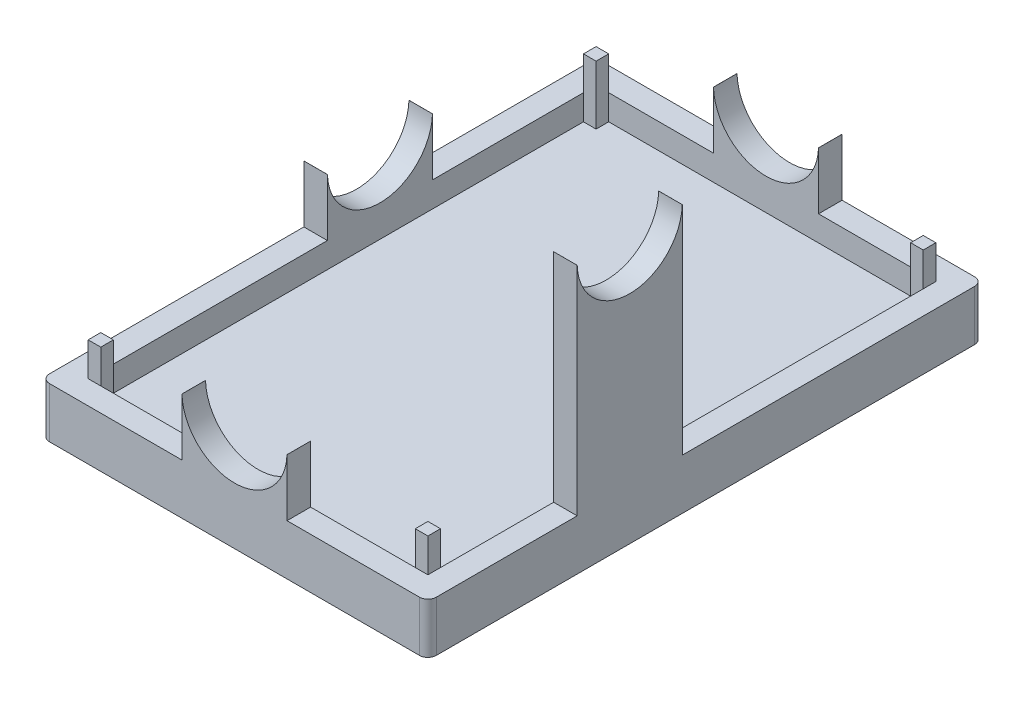
SolidWorks part; units mm, degrees
ref_plane "Front Plane" through (0, 0, 0) normal (0, 0, 1) x (1, 0, 0)
ref_plane "Top Plane" through (0, 0, 0) normal (0, 1, 0) x (1, 0, 0)
ref_plane "Right Plane" through (0, 0, 0) normal (1, 0, 0) x (0, 0, -1)
sketch "Sketch1" plane through (0, 0, 0) normal (0, 1, 0) x (1, 0, 0)
  line L1 (4.944, 70.2935) -> (50.944, 70.2935)
  line L2 (4.944, 70.2935) -> (4.944, 4.2935)
  line L3 (4.944, 4.2935) -> (50.944, 4.2935)
  line L4 (50.944, 70.2935) -> (50.944, 4.2935)
extrude "Boss-Extrude1" add sketch "Sketch1" along normal blind 3 contours L2 L1 L4 L3
sketch "Sketch2" plane through (0, 3, 0) normal (0, 1, 0) x (1, 0, 0)
  line L0 (50.944, 70.2935) -> (50.944, 4.2935) construction
  line L1 (4.944, 70.2935) -> (50.944, 70.2935) construction
  line L2 (4.944, 4.2935) -> (50.944, 4.2935) construction
  line L7 (7.944, 70.2935) -> (50.944, 70.2935)
  line L8 (7.944, 70.2935) -> (7.944, 67.2935)
  line L9 (7.944, 67.2935) -> (50.944, 67.2935)
  line L10 (50.944, 70.2935) -> (50.944, 67.2935)
  line L12 (50.944, 67.2935) -> (47.944, 67.2935)
  line L13 (50.944, 67.2935) -> (50.944, 4.2935)
  line L14 (50.944, 4.2935) -> (47.944, 4.2935)
  line L15 (47.944, 67.2935) -> (47.944, 4.2935)
  line L20 (7.944, 4.2935) -> (47.944, 4.2935)
  line L21 (7.944, 4.2935) -> (7.944, 7.2935)
  line L22 (7.944, 7.2935) -> (47.944, 7.2935)
  line L23 (47.944, 4.2935) -> (47.944, 7.2935)
  line L24 (4.944, 70.2935) -> (7.944, 70.2935)
  line L25 (4.944, 70.2935) -> (4.944, 4.2935)
  line L26 (4.944, 4.2935) -> (7.944, 4.2935)
  line L27 (7.944, 70.2935) -> (7.944, 4.2935)
extrude "Boss-Extrude2" add sketch "Sketch2" along normal blind 3 contours L25 L24 L27 L26 | L21 L20 L23 L22 | L13 L12 L15 L14 | L8 L7 L10 L9
sketch "Sketch3" plane through (7.944, 0, 0) normal (1, 0, 0) x (0, 0, -1)
  line L1 (7.2935, 3) -> (67.2935, 3)
  line L2 (7.2935, 3) -> (7.2935, 6)
  line L3 (7.2935, 6) -> (67.2935, 6)
  line L4 (67.2935, 3) -> (67.2935, 6)
extrude "Cut-Extrude1" cut sketch "Sketch3" against normal blind 0.2 contours L2 L1 L4 L3
sketch "Sketch4" plane through (0, 0, -7.2935) normal (0, 0, -1) x (-1, 0, 0)
  line L1 (-47.944, 3) -> (-7.744, 3)
  line L2 (-47.944, 3) -> (-47.944, 6)
  line L3 (-47.944, 6) -> (-7.744, 6)
  line L4 (-7.744, 3) -> (-7.744, 6)
extrude "Cut-Extrude2" cut sketch "Sketch4" against normal blind 0.2
sketch "Sketch5" plane through (47.944, 0, 0) normal (-1, 0, 0) x (0, 0, 1)
  line L1 (-67.2935, 3) -> (-7.0935, 3)
  line L2 (-67.2935, 3) -> (-67.2935, 6)
  line L3 (-67.2935, 6) -> (-7.0935, 6)
  line L4 (-7.0935, 3) -> (-7.0935, 6)
extrude "Cut-Extrude3" cut sketch "Sketch5" against normal blind 0.2
sketch "Sketch6" plane through (0, 0, -67.2935) normal (0, 0, 1) x (1, 0, 0)
  line L1 (7.744, 3) -> (48.144, 3)
  line L2 (7.744, 3) -> (7.744, 6)
  line L3 (7.744, 6) -> (48.144, 6)
  line L4 (48.144, 3) -> (48.144, 6)
extrude "Cut-Extrude4" cut sketch "Sketch6" against normal blind 0.2
sketch "Sketch8" plane through (0, 6, 0) normal (0, 1, 0) x (1, 0, 0)
  line L2 (27.944, 7.0935) -> (34.194, 7.0935)
  line L9 (48.144, 7.0935) -> (7.744, 7.0935) construction
  line L10 (27.944, 7.0935) -> (21.694, 7.0935)
  line L11 (7.744, 7.0935) -> (48.144, 7.0935) construction
  line L12 (21.694, 7.0935) -> (21.694, 4.2935)
  line L13 (4.944, 4.2935) -> (50.944, 4.2935) construction
  line L14 (21.694, 4.2935) -> (34.194, 4.2935)
  line L15 (34.194, 4.2935) -> (34.194, 7.0935)
extrude "Boss-Extrude3" add sketch "Sketch8" along normal blind 6.8 contours L15 L2 L10 L12 L14
sketch "Sketch10" plane through (0, 6, 0) normal (0, 1, 0) x (1, 0, 0)
  line L0 (27.944, 67.4935) -> (34.194, 67.4935)
  line L1 (7.744, 67.4935) -> (48.144, 67.4935) construction
  line L2 (27.944, 67.4935) -> (21.694, 67.4935)
  line L3 (21.694, 67.4935) -> (21.694, 70.2935)
  line L4 (4.944, 70.2935) -> (50.944, 70.2935) construction
  line L5 (21.694, 70.2935) -> (34.194, 70.2935)
  line L6 (34.194, 70.2935) -> (34.194, 67.4935)
extrude "Boss-Extrude4" add sketch "Sketch10" along normal blind 6.8 contours L6 L0 L2 L3 L5
sketch "Sketch11" plane through (0, 0, -4.2935) normal (0, 0, 1) x (1, 0, 0)
  circle A0 centre (27.944, 13) radius 6.25
  point P5 (0, 0)
extrude "Cut-Extrude5" cut sketch "Sketch11" against normal blind 66 contours A0
sketch "Sketch12" plane through (0, 6, 0) normal (0, 1, 0) x (1, 0, 0)
  line L0 (7.744, 48.0435) -> (4.944, 48.0435)
  line L1 (4.944, 70.2935) -> (4.944, 4.2935) construction
  line L3 (7.744, 7.0935) -> (7.744, 67.4935) construction
  line L4 (7.744, 41.7935) -> (7.744, 48.0435)
  line L5 (7.744, 7.0935) -> (7.744, 67.4935) construction
  line L6 (7.744, 41.7935) -> (7.744, 35.5435)
  line L7 (7.744, 35.5435) -> (4.944, 35.5435)
  line L9 (4.944, 48.0435) -> (4.944, 35.5435)
extrude "Boss-Extrude5" add sketch "Sketch12" along normal blind 6.8 contours L9 L7 L6 L4 L0
sketch "Sketch13" plane through (4.944, 0, 0) normal (-1, 0, 0) x (0, 0, 1)
  circle A0 centre (-41.7935, 13) radius 6.25
extrude "Cut-Extrude6" cut sketch "Sketch13" against normal blind 3 contours A0
sketch "Sketch14" plane through (0, 6, 0) normal (0, 1, 0) x (1, 0, 0)
  line L6 (50.944, 70.2935) -> (50.944, 4.2935) construction
  line L12 (48.144, 67.4935) -> (48.144, 7.0935) construction
  line L13 (50.944, 22.0435) -> (48.144, 22.0435)
  line L14 (50.944, 22.0435) -> (50.944, 34.5435)
  line L15 (50.944, 34.5435) -> (48.144, 34.5435)
  line L16 (48.144, 22.0435) -> (48.144, 34.5435)
extrude "Boss-Extrude6" add sketch "Sketch14" along normal blind 25.8 contours L14 L13 L16 L15
sketch "Sketch15" plane through (50.944, 0, 0) normal (1, 0, 0) x (0, 0, -1)
  circle A0 centre (28.2935, 32) radius 6.25
extrude "Cut-Extrude7" cut sketch "Sketch15" against normal blind 4.8 contours A0
sketch "Sketch16" plane through (0, 3, 0) normal (0, 1, 0) x (1, 0, 0)
  line L1 (7.744, 67.4935) -> (9.244, 67.4935)
  line L2 (7.744, 67.4935) -> (7.744, 65.9935)
  line L3 (7.744, 65.9935) -> (9.244, 65.9935)
  line L4 (9.244, 67.4935) -> (9.244, 65.9935)
  line L9 (48.144, 67.4935) -> (46.644, 67.4935)
  line L10 (48.144, 67.4935) -> (48.144, 65.9935)
  line L11 (48.144, 65.9935) -> (46.644, 65.9935)
  line L12 (46.644, 67.4935) -> (46.644, 65.9935)
  line L13 (48.144, 7.0935) -> (46.644, 7.0935)
  line L14 (48.144, 7.0935) -> (48.144, 8.5935)
  line L15 (48.144, 8.5935) -> (46.644, 8.5935)
  line L16 (46.644, 7.0935) -> (46.644, 8.5935)
  line L17 (7.744, 7.0935) -> (9.244, 7.0935)
  line L18 (7.744, 7.0935) -> (7.744, 8.5935)
  line L19 (7.744, 8.5935) -> (9.244, 8.5935)
  line L20 (9.244, 7.0935) -> (9.244, 8.5935)
extrude "Boss-Extrude7" add sketch "Sketch16" along normal blind 7 contours L2 L1 L4 L3 | L10 L9 L12 L11 | L14 L13 L16 L15 | L18 L17 L20 L19
fillet "Fillet1" radius 1 4 edges at (4.944, 3, -70.2935) (50.944, 3, -70.2935) (50.944, 3, -4.2935) (4.944, 3, -4.2935)
sketch "Sketch17" plane through (0, 0, 0) normal (0, -1, 0) x (1, 0, 0)
  text T0 "<i>2H T/R Switch</i>"
extrude "Cut-Extrude8" cut sketch "Sketch17" against normal blind 0.2
